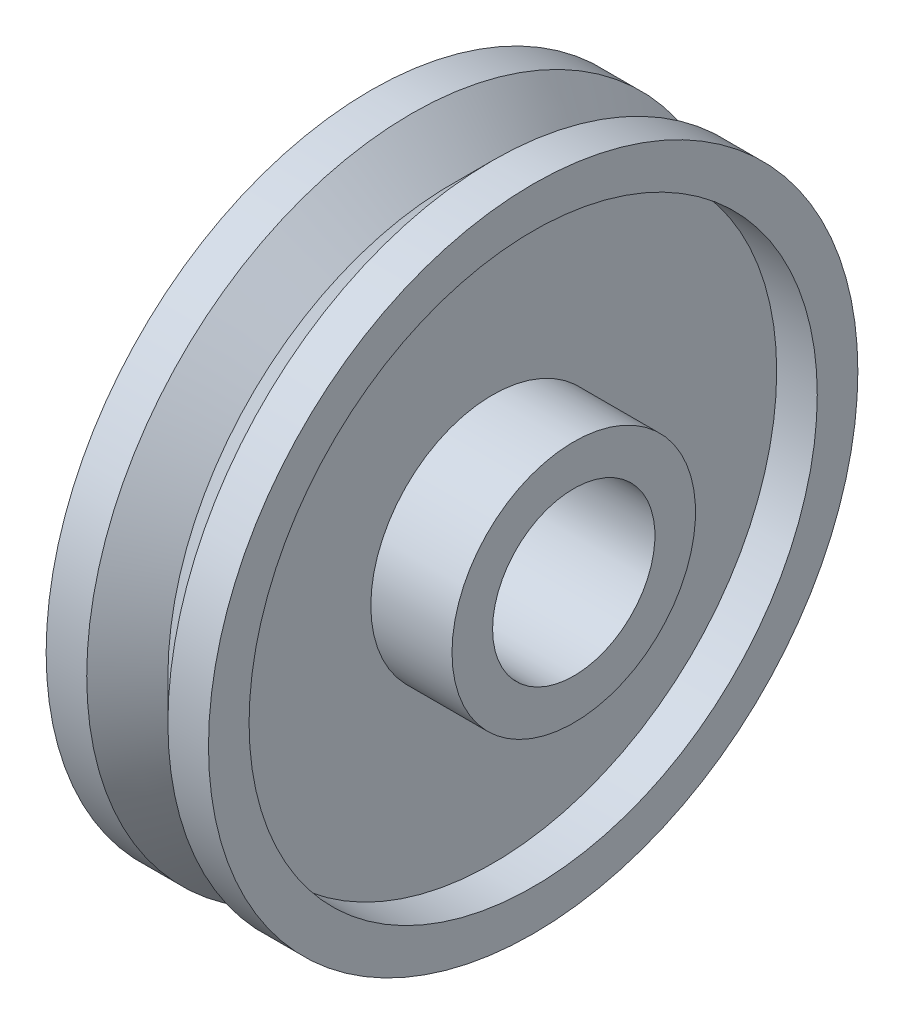
SolidWorks part; units mm, degrees
ref_plane "Front Plane" through (0, 0, 0) normal (0, 0, 1) x (1, 0, 0)
ref_plane "Top Plane" through (0, 0, 0) normal (0, 1, 0) x (1, 0, 0)
ref_plane "Right Plane" through (0, 0, 0) normal (1, 0, 0) x (0, 0, -1)
sketch "Sketch1" plane through (0, 0, 0) normal (0, 0, 1) x (1, 0, 0)
  line L0 (-487.0325, 0) -> (23864.5939, 0) construction
  line L1 (0, -487.0325) -> (0, 23864.5939) construction
  line L2 (-19.05, 12.7) -> (19.05, 12.7)
  line L3 (19.05, 12.7) -> (19.05, 19.05)
  line L4 (19.05, 19.05) -> (6.35, 19.05)
  line L5 (6.35, 19.05) -> (6.35, 44.45)
  line L6 (6.35, 44.45) -> (12.7, 44.45)
  line L7 (12.7, 44.45) -> (12.7, 50.8)
  line L8 (12.7, 50.8) -> (6.35, 50.8)
  line L9 (6.35, 50.8) -> (0, 44.45)
  line L10 (-6.35, 50.8) -> (0, 44.45)
  line L11 (-12.7, 50.8) -> (-6.35, 50.8)
  line L12 (-12.7, 44.45) -> (-12.7, 50.8)
  line L13 (-6.35, 44.45) -> (-12.7, 44.45)
  line L14 (-6.35, 19.05) -> (-6.35, 44.45)
  line L15 (-19.05, 19.05) -> (-6.35, 19.05)
  line L16 (-19.05, 12.7) -> (-19.05, 19.05)
  point P22 (0, 12.7)
  dimension "D1" = 50.8
  dimension "D2" = 44.45
  dimension "D3" = 19.05
  dimension "D4" = 12.7
  dimension "D5" = 6.35
  dimension "D6" = 19.05
  dimension "D7" = 12.7
  dimension "D8" = 45
revolve "Revolve1" add sketch "Sketch1" angle 360 about L0
